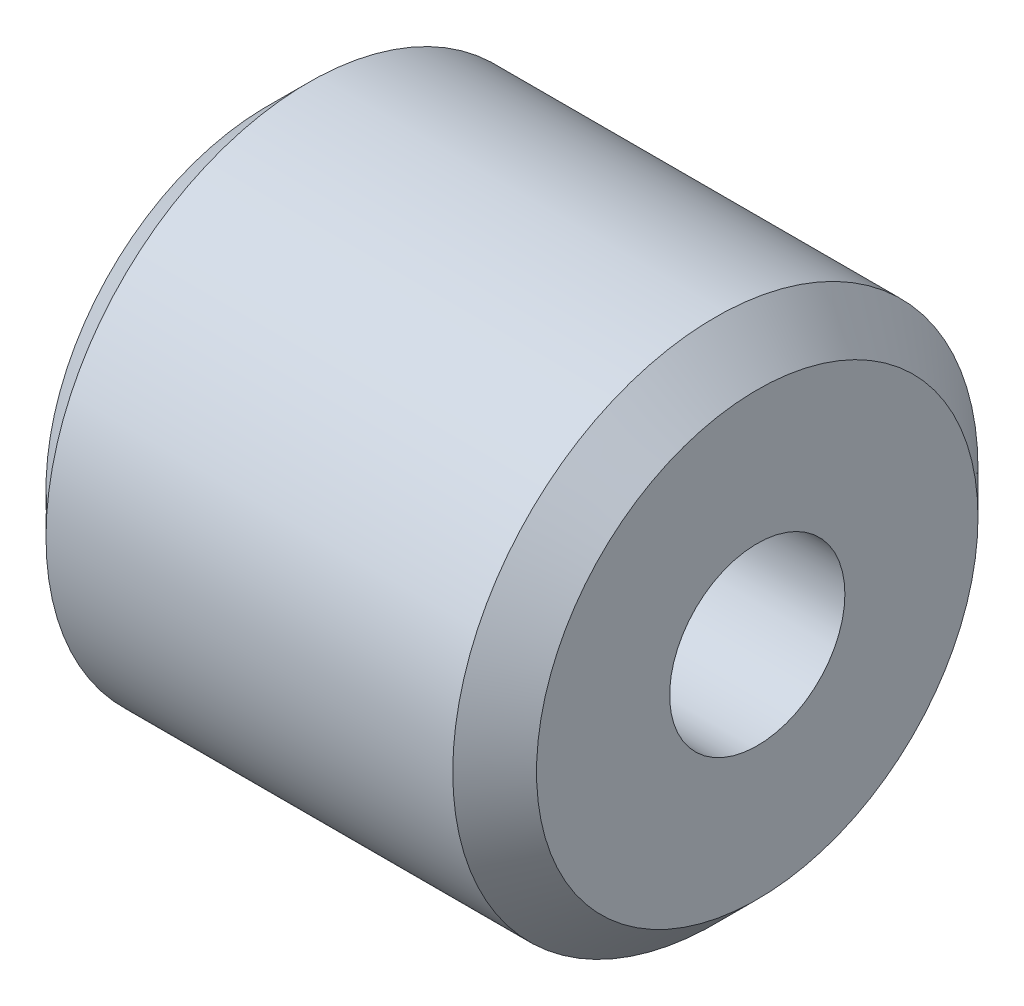
SolidWorks part; units mm, degrees
ref_plane "Front Plane" through (0, 0, 0) normal (0, 0, 1) x (1, 0, 0)
ref_plane "Top Plane" through (0, 0, 0) normal (0, 1, 0) x (1, 0, 0)
ref_plane "Right Plane" through (0, 0, 0) normal (1, 0, 0) x (0, 0, -1)
sketch "Sketch1" plane through (0, 0, 0) normal (1, 0, 0) x (0, 0, -1)
  circle A0 centre (0, 0) radius 4.765
  circle A1 centre (0, 0) radius 1.59
  dimension "D1" = 3.18
  dimension "D2" = 9.53
extrude "Boss-Extrude1" add sketch "Sketch1" along normal mid plane 8.9
chamfer "Chamfer1" distance 0.76 angle 45 2 edges at (-4.45, 0, -4.765) (4.45, 0, -4.765)
